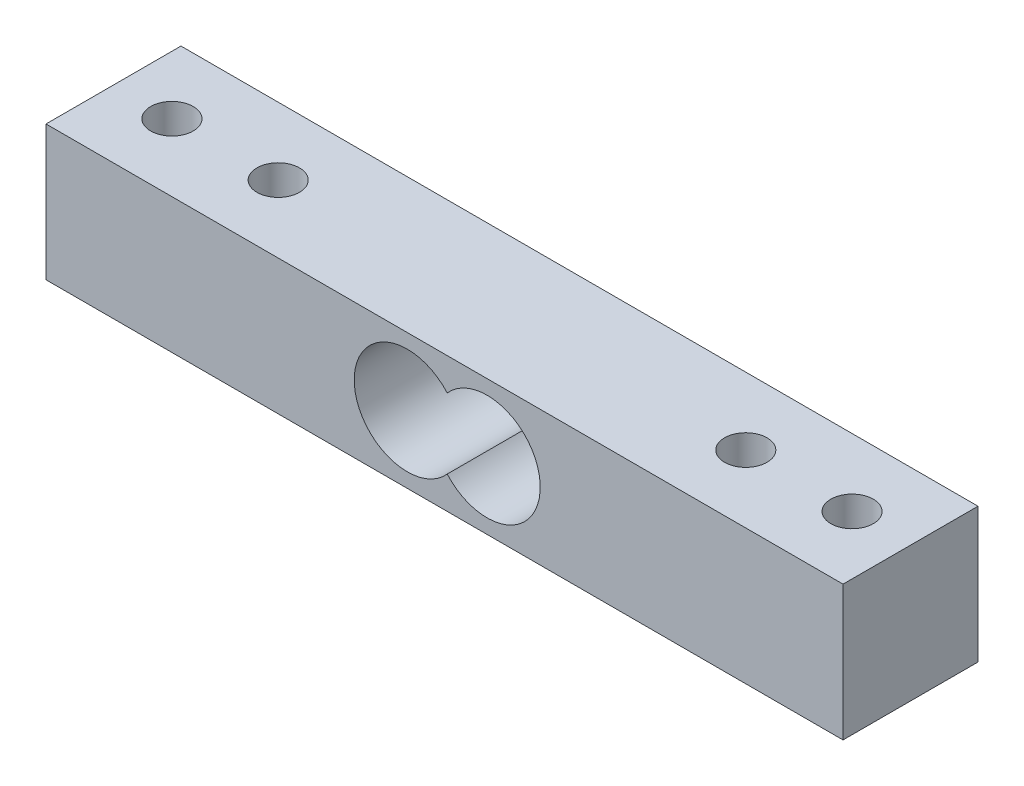
SolidWorks part; units mm, degrees
ref_plane "Front Plane" through (0, 0, 0) normal (0, 0, 1) x (1, 0, 0)
ref_plane "Top Plane" through (0, 0, 0) normal (0, 1, 0) x (1, 0, 0)
ref_plane "Right Plane" through (0, 0, 0) normal (1, 0, 0) x (0, 0, -1)
sketch "Sketch1" plane through (0, 0, 0) normal (0, 1, 0) x (1, 0, 0)
  line L1 (37.5, -6.35) -> (-37.5, -6.35)
  line L2 (37.5, -6.35) -> (37.5, 6.35)
  line L3 (37.5, 6.35) -> (-37.5, 6.35)
  line L4 (-37.5, -6.35) -> (-37.5, 6.35)
  line L5 (37.5, -6.35) -> (-37.5, 6.35) construction
  line L6 (37.5, 6.35) -> (-37.5, -6.35) construction
  circle A0 centre (-32, 0) radius 2
  circle A1 centre (-22, 0) radius 2
  circle A2 centre (22, 0) radius 2
  circle A3 centre (32, 0) radius 2
  point P0 (0, 0)
  dimension "D3" = 4
  dimension "D4" = 4
  dimension "D5" = 4
  dimension "D6" = 4
  dimension "D7" = 10
  dimension "D8" = 10
  dimension "D9" = 44
  dimension "D10" = 22
  dimension "D1" = 75
  dimension "D2" = 12.7
extrude "Boss-Extrude1" add sketch "Sketch1" along normal blind 12.7
sketch "Sketch2" plane through (0, 0, 6.35) normal (0, 0, 1) x (1, 0, 0)
  line L0 (-37.5, 6.35) -> (37.5, 6.35) construction
  line L1 (-37.5, 12.7) -> (-37.5, 0) construction
  line L2 (37.5, 12.7) -> (37.5, 0) construction
  circle A0 centre (-3.5, 6.35) radius 5
  circle A1 centre (4.0058, 6.35) radius 5
  point P13 (-3.5, 1.35)
  dimension "D3" = 10
  dimension "D4" = 10
  dimension "D1" = 4.0058
  dimension "D2" = 3.5
extrude "Cut-Extrude1" cut sketch "Sketch2" against normal blind 12.7 contours A0 L0 A1 | L0 A0 A1 | A1 L0 A0 | L0 A1 A0 | L0 A0 A1 | A0 L0 A1
